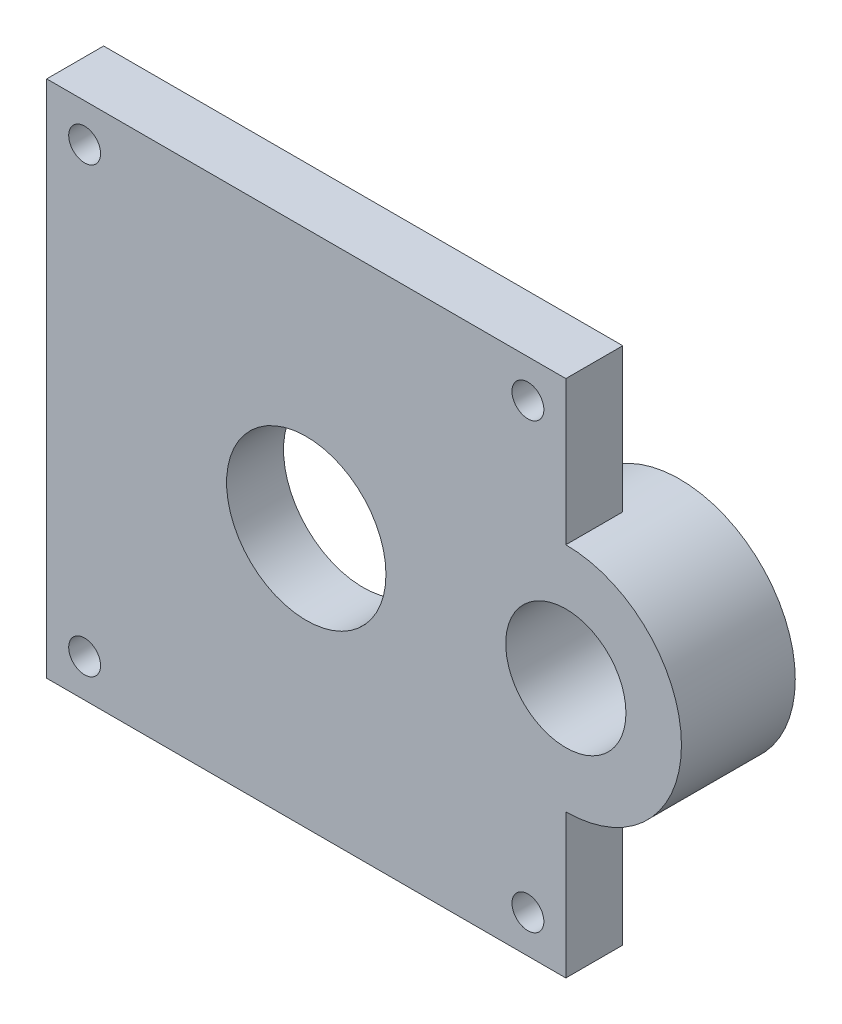
SolidWorks part; units mm, degrees
ref_plane "Front" through (0, 0, 0) normal (0, 0, 1) x (1, 0, 0)
ref_plane "Top" through (0, 0, 0) normal (0, 1, 0) x (1, 0, 0)
ref_plane "Right" through (0, 0, 0) normal (1, 0, 0) x (0, 0, -1)
sketch "Sketch1" plane through (0, 0, 0) normal (0, 0, 1) x (1, 0, 0)
  line L1 (0, 0) -> (28.956, 0)
  line L2 (0, 0) -> (0, 28.956)
  line L3 (0, 28.956) -> (28.956, 28.956)
  line L4 (28.956, 0) -> (28.956, 28.956)
  circle A0 centre (14.478, 14.478) radius 4.445
  dimension "D4" = 8.89
  dimension "D1" = 28.956
  dimension "D2" = 14.478
  dimension "D3" = 14.478
extrude "Boss-Extrude1" add sketch "Sketch1" along normal blind 3.175
sketch "Sketch2" plane through (0, 0, 3.175) normal (0, 0, 1) x (1, 0, 0)
  line L0 (0, 0) -> (28.956, 0) construction
  line L1 (0, 28.956) -> (0, 0) construction
  line L2 (0, 14.478) -> (28.956, 14.478) construction
  line L3 (28.956, 0) -> (28.956, 28.956) construction
  line L4 (14.478, 0) -> (14.478, 28.956) construction
  line L5 (28.956, 28.956) -> (0, 28.956) construction
  circle A0 centre (2.1146, 2.1145) radius 0.889
  circle A1 centre (26.8414, 2.1145) radius 0.889
  circle A2 centre (26.8414, 26.8414) radius 0.889
  circle A3 centre (2.1146, 26.8414) radius 0.889
  dimension "D1" = 1.778
  dimension "D2" = 2.1146
  dimension "D3" = 2.1146
extrude "Cut-Extrude1" cut sketch "Sketch2" against normal through all
sketch "Sketch3" plane through (0, 0, 3.175) normal (0, 0, 1) x (1, 0, 0)
  line L0 (18.923, 14.478) -> (28.956, 14.478) construction
  line L1 (28.956, 0) -> (28.956, 28.956) construction
  line L2 (23.9395, 28.956) -> (23.9395, 0) construction
  line L3 (0, 0) -> (28.956, 0) construction
  circle A0 centre (14.478, 14.478) radius 4.445 construction
  circle A1 centre (28.956, 14.478) radius 3.2742 construction
  circle A2 centre (28.956, 14.478) radius 6.4492
  point P11 (23.9395, 14.478)
  dimension "D1" = 6.5484
  dimension "D2" = 3.175
extrude "Boss-Extrude2" add sketch "Sketch3" against normal blind 6.35
sketch "Sketch4" plane through (0, 0, 3.175) normal (0, 0, 1) x (1, 0, 0)
  line L0 (28.956, 28.956) -> (28.956, 0) construction
  circle A0 centre (28.956, 14.478) radius 3.3528
  dimension "D1" = 6.7056
extrude "Cut-Extrude2" cut sketch "Sketch4" against normal through all
